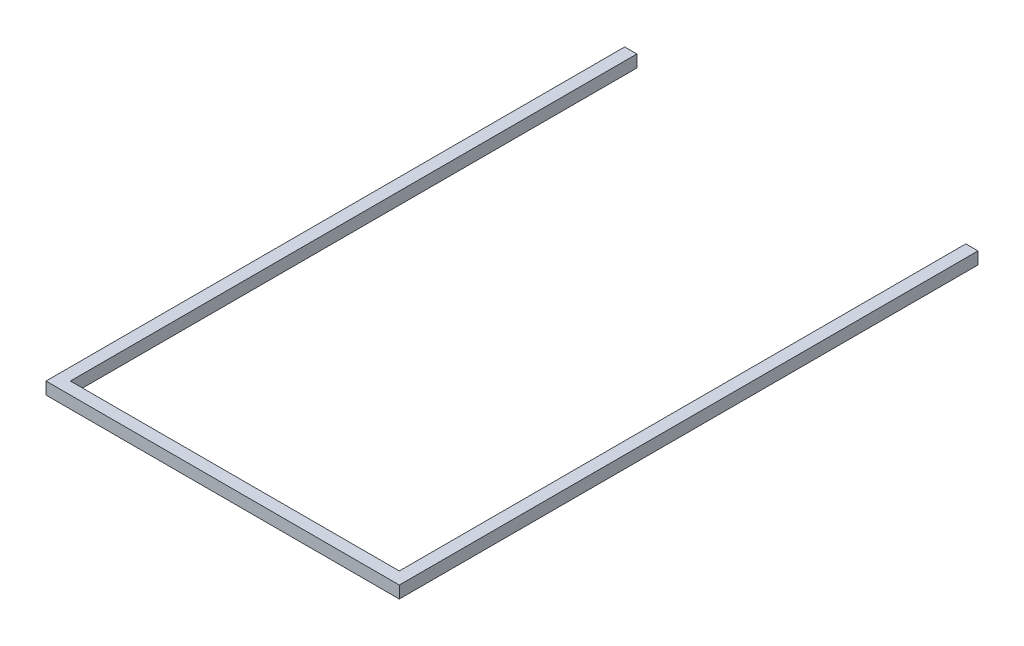
SolidWorks part; units mm, degrees
ref_plane "Front Plane" through (0, 0, 0) normal (0, 0, 1) x (1, 0, 0)
ref_plane "Top Plane" through (0, 0, 0) normal (0, 1, 0) x (1, 0, 0)
ref_plane "Right Plane" through (0, 0, 0) normal (1, 0, 0) x (0, 0, -1)
sketch "Sketch1" plane through (0, 0, 0) normal (0, 1, 0) x (1, 0, 0)
  line L0 (-81.1443, 891.7878) -> (-81.1443, -58.2122)
  line L1 (-81.1443, -58.2122) -> (498.8557, -58.2122)
  line L2 (498.8557, -58.2122) -> (498.8557, 891.7878)
  line L3 (498.8557, 891.7878) -> (478.8557, 891.7878)
  line L4 (478.8557, 891.7878) -> (478.8557, -38.2122)
  line L5 (478.8557, -38.2122) -> (-61.1443, -38.2122)
  line L6 (-61.1443, -38.2122) -> (-61.1443, 891.7878)
  line L7 (-61.1443, 891.7878) -> (-81.1443, 891.7878)
  line L8 (-61.1443, -38.2122) -> (-61.1443, -58.2122) construction
  dimension "D1" = 950
  dimension "D2" = 20
  dimension "D3" = 580
extrude "Boss-Extrude1" add sketch "Sketch1" along normal blind 20
